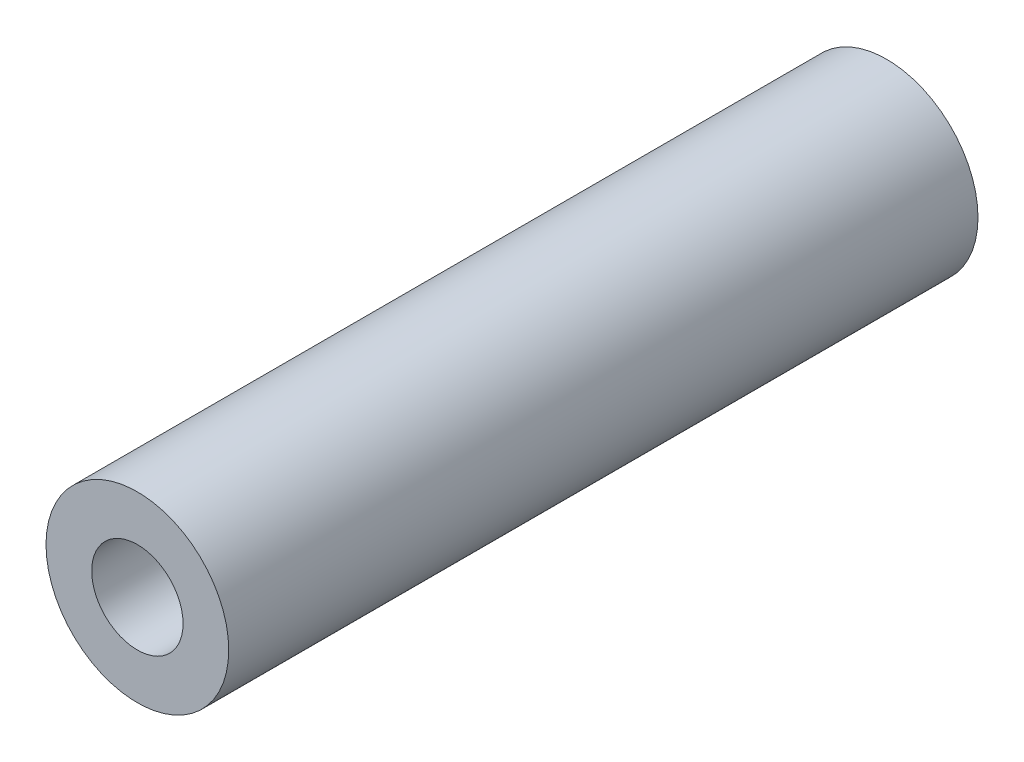
SolidWorks part; units mm, degrees
ref_plane "Front" through (0, 0, 0) normal (0, 0, 1) x (1, 0, 0)
ref_plane "Top" through (0, 0, 0) normal (0, 1, 0) x (1, 0, 0)
ref_plane "Right" through (0, 0, 0) normal (1, 0, 0) x (0, 0, -1)
sketch "Sketch1" plane through (0, 0, 0) normal (0, 0, 1) x (1, 0, 0)
  circle A0 centre (0, 0) radius 3.175
  circle A1 centre (0, 0) radius 6.35
  dimension "D1" = 12.7
  dimension "D2" = 6.35
extrude "Boss-Extrude1" add sketch "Sketch1" along normal blind 52.07
